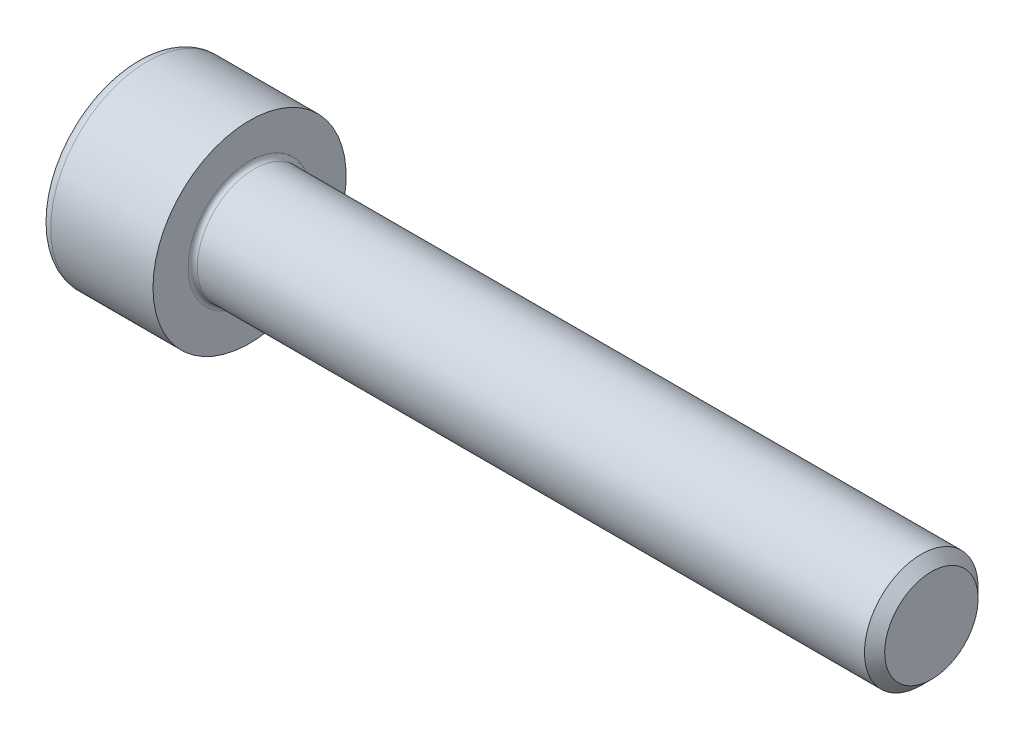
SolidWorks part; units mm, degrees
revolve "Base-Revolve" add sketch "BodySke"
sketch "BodySke" plane through (0, 0, 0) normal (0, 0, 1) x (1, 0, 0)
  line L0 (0, 0) -> (0, 4.25)
  line L1 (0, 4.25) -> (5, 4.25)
  line L2 (5, 4.25) -> (5, 2.5)
  line L3 (5, 2.5) -> (34.555, 2.5)
  line L4 (35, 2.055) -> (35, 0)
  line L5 (35, 0) -> (0, 0)
  line L6 (-31.75, 0) -> (127, 0) construction
  line L8 (35, 2.055) -> (34.555, 2.5)
  line L10 (35, -2.055) -> (34.555, -2.5) construction
  line L11 (5.8, 9.525) -> (5.8, 3.175) construction
  line L12 (5, 9.525) -> (5, 3.175) construction
  line L13 (-25, 9.525) -> (-25, 3.175) construction
  dimension "Head_ht" = 5
  dimension "Length" = 30
  dimension "Body_ch_ang" = 45
  dimension "Diameter" = 5
  dimension "Minor_dia" = 4.11
  dimension "Advance" = 0.8
  dimension "Thread_nom" = 30
  dimension "Thread_length" = 60
  dimension "Head_dia" = 8.5
cosmetic thread "ThreadCosmetic"
fillet "Fillet1" radius 0.2 1 edges at (5, 0, 2.5)
fillet "Fillet2" radius 0.5 1 edges at (0, 0, 4.25)
ref_plane "Plane1" through (0, 0, 0) normal (0, 0, 1) x (1, 0, 0)
ref_plane "Plane2" through (0, 0, 0) normal (0, 1, 0) x (1, 0, 0)
ref_plane "Plane3" through (0, 0, 0) normal (1, 0, 0) x (0, 0, -1)
sketch "Sketch2" plane through (0, 0, 0) normal (0, 0, 1) x (1, 0, 0)
  line L0 (0, 2.01) -> (2.5, 2.01)
  line L1 (2.5, 2.01) -> (3.6605, 0)
  line L2 (-31.75, 0) -> (127, 0) construction
  line L3 (3.6605, 0) -> (0, 0)
  line L4 (0, 0) -> (0, 2.01)
  line L6 (0, 0) -> (47.625, 0) construction
  dimension "D1" = 2.01
  dimension "D2" = 60
  dimension "Depth" = 2.5
revolve "Hex-PreBroach" cut sketch "Sketch2" angle 360 about L6
sketch "Sketch3" plane through (0, 0, 0) normal (-1, 0, 0) x (0, 0.5, 0.866)
  line L0 (1.1605, 2.01) -> (-1.1605, 2.01)
  line L1 (-1.1605, 2.01) -> (-2.3209, 0)
  line L2 (1.1605, 2.01) -> (2.3209, 0)
  line L3 (1.1605, -2.01) -> (2.3209, 0)
  line L4 (1.1605, -2.01) -> (-1.1605, -2.01)
  line L5 (-1.1605, -2.01) -> (-2.3209, 0)
  dimension "D1" = 2.01
  dimension "D2" = 2.01
  dimension "Hex_size" = 4.02
extrude "Hex" cut sketch "Sketch3" against normal blind 2.5
sketch "ThdSchSke" plane through (0, 0, 0) normal (0, 0, 1) x (1, 0, 0)
  line L0 (7.4, -2.055) -> (7.0884, -2.5)
  line L1 (7.4, -2.055) -> (7.7116, -2.5)
  line L2 (7.7116, -2.5) -> (7.7116, -3.125)
  line L3 (-3.175, 0) -> (5.1513, 0) construction
  line L4 (0, 3.75) -> (0, -3.75) construction
  line L5 (7.7116, -3.125) -> (7.0884, -3.125)
  line L6 (7.0884, -3.125) -> (7.0884, -2.5)
  dimension "Thread_minor" = 4.11
  dimension "Diameter" = 5
  dimension "Start" = 7.4
revolve "ThreadSchematic" [suppressed] cut sketch "ThdSchSke" angle 360 about L3
pattern_linear "ThdSchPat" [suppressed]
equation "\"D2@Sketch3\" = \"Hex_size@Sketch3\" / 2"
equation "\"D1@Sketch3\" = \"Hex_size@Sketch3\" / 2"
equation "\"D1@Sketch2\" = \"Hex_size@Sketch3\" / 2"
equation "\"Thread_minor@ThreadCosmetic\"  =  \"Minor_dia@BodySke\""
equation "\"Depth@Sketch2\" =  \"Key_eng@Hex\""
equation "\"Thread_length@ThreadCosmetic\" = ((sgn( (\"Length@BodySke\" - \"Advance@BodySke\" * 3.0) - \"Thread_nom@BodySke\" )-1)*( (\"Length@BodySke\" - \"Advance@BodySke\" * 3.0) - \"Thread_nom@BodySke\" ))/-2+ \"Thread_nom@BodySke\""
equation "\"Thread_minor@ThdSchSke\" = \"Minor_dia@BodySke\""
equation "\"Diameter@ThdSchSke\" = \"Diameter@BodySke\""
equation "\"Overcut@ThdSchSke\" = \"Diameter@BodySke\" * 1.25"
equation "\"Start@ThdSchSke\" = \"Head_ht@BodySke\" + \"Length@BodySke\" - \"Thread_length@ThreadCosmetic\"  '---Non-countersunk---"
equation "\"Num_threads@ThdSchPat\" = int( \"Thread_length@ThreadCosmetic\" / \"Advance@BodySke\" + 0.999 )  + 1"
equation "\"Advance@ThdSchPat\" = \"Thread_length@ThreadCosmetic\" /  (\"Num_threads@ThdSchPat\" - 1) 'relax it"
equation "\"Num_threads@ThdSchPat\" = \"Num_threads@ThdSchPat\" - sgn( \"Num_threads@ThdSchPat\" - 1) '---chamfered tips only---"
